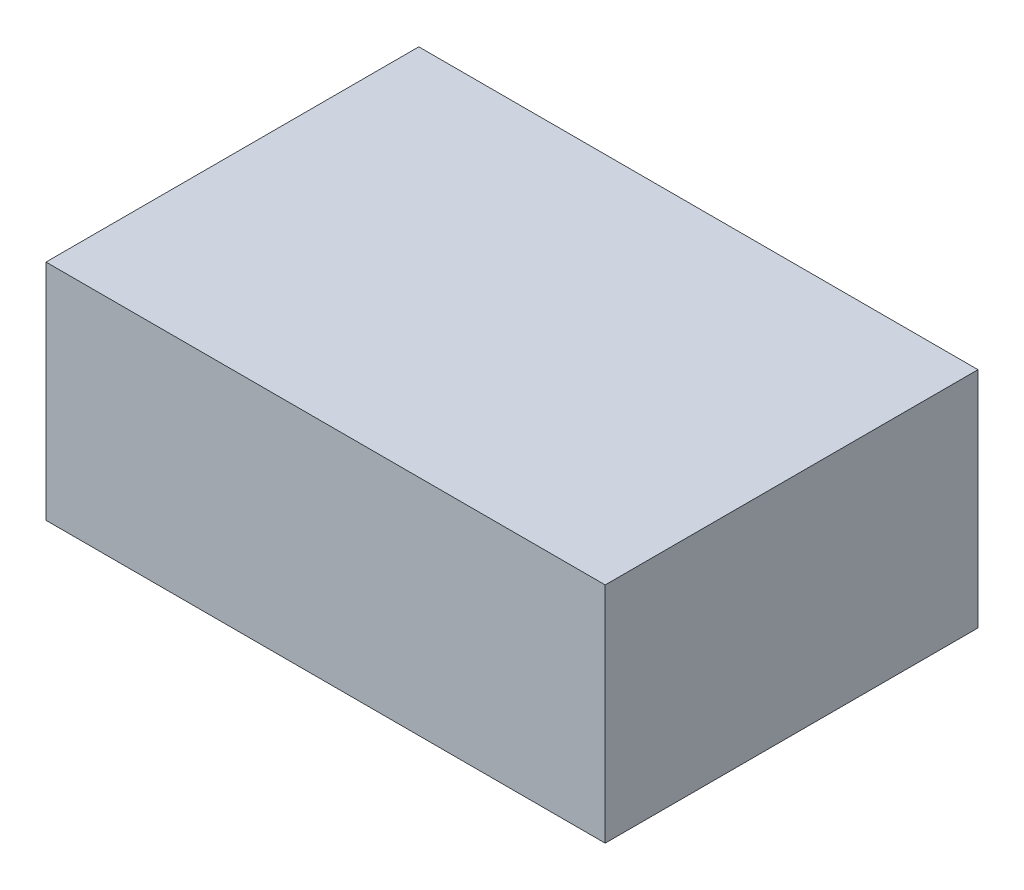
SolidWorks part; units mm, degrees
ref_plane "Front Plane" through (0, 0, 0) normal (0, 0, 1) x (1, 0, 0)
ref_plane "Top Plane" through (0, 0, 0) normal (0, 1, 0) x (1, 0, 0)
ref_plane "Right Plane" through (0, 0, 0) normal (1, 0, 0) x (0, 0, -1)
sketch "Sketch1" plane through (0, 0, 0) normal (0, 1, 0) x (1, 0, 0)
  line L1 (-150, 100) -> (150, 100)
  line L2 (-150, 100) -> (-150, -100)
  line L3 (-150, -100) -> (150, -100)
  line L4 (150, 100) -> (150, -100)
  line L5 (0, -100) -> (0, 100) construction
  line L6 (-150, 0) -> (150, 0) construction
  point P0 (0, 0)
  dimension "D1" = 300
  dimension "D2" = 200
extrude "Boss-Extrude1" add sketch "Sketch1" along normal blind 120
